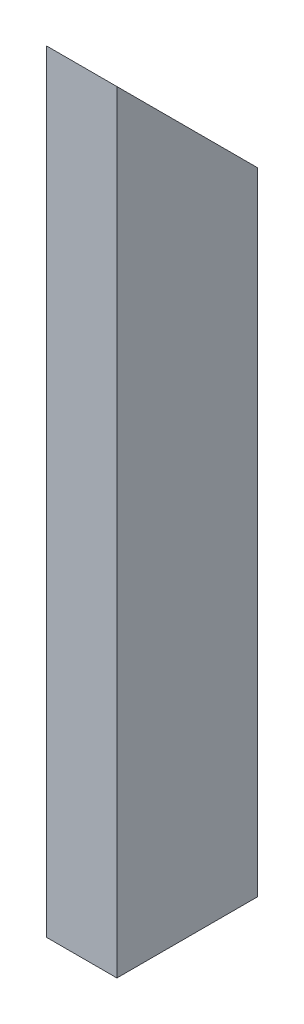
SolidWorks part; units mm, degrees
ref_plane "Front Plane" through (0, 0, 0) normal (0, 0, 1) x (1, 0, 0)
ref_plane "Top Plane" through (0, 0, 0) normal (0, 1, 0) x (1, 0, 0)
ref_plane "Right Plane" through (0, 0, 0) normal (1, 0, 0) x (0, 0, -1)
sketch "Sketch1" plane through (0, 0, 0) normal (0, 1, 0) x (1, 0, 0)
  line L1 (0, 0) -> (25.4, 0)
  line L2 (0, 0) -> (0, 50.8)
  line L3 (0, 50.8) -> (25.4, 50.8)
  line L4 (25.4, 0) -> (25.4, 50.8)
  line L5 (3.175, 3.175) -> (22.225, 3.175)
  line L6 (3.175, 3.175) -> (3.175, 47.625)
  line L7 (3.175, 47.625) -> (22.225, 47.625)
  line L8 (22.225, 3.175) -> (22.225, 47.625)
  dimension "D1" = 25.4
  dimension "D2" = 50.8
  dimension "D3" = 3.175
  dimension "D4" = 3.175
  dimension "D5" = 3.175
  dimension "D6" = 3.175
extrude "Boss-Extrude1" add sketch "Sketch1" along normal blind 279.4
sketch "Sketch2" plane through (25.4, 0, 0) normal (1, 0, 0) x (0, 0, -1)
  line L0 (0, 279.4) -> (50.8, 228.6)
  line L1 (50.8, 279.4) -> (50.8, 0) construction
  line L3 (0, 279.4) -> (50.8, 279.4)
  line L4 (50.8, 279.4) -> (50.8, 228.6)
  dimension "D1" = 228.6
extrude "Cut-Extrude1" cut sketch "Sketch2" against normal blind 279.4
